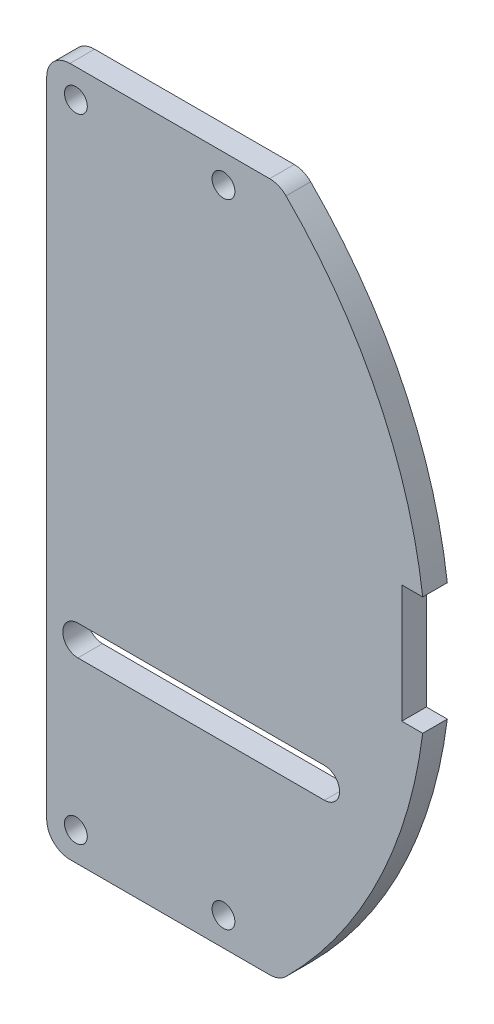
SolidWorks part; units mm, degrees
material "Delrin 2700 NC010, Low Viscosity Acetal Copolymer (SS)"
ref_plane "Front Plane" through (0, 0, 0) normal (0, 0, 1) x (1, 0, 0)
ref_plane "Top Plane" through (0, 0, 0) normal (0, 1, 0) x (1, 0, 0)
ref_plane "Right Plane" through (0, 0, 0) normal (1, 0, 0) x (0, 0, -1)
sketch "Sketch1" plane through (0, 0, 0) normal (0, 0, 1) x (1, 0, 0)
  line L2 (12.5875, 44.5) -> (42.5875, 44.5)
  line L5 (12.5875, -44.5) -> (12.5875, 44.5)
  line L8 (12.5875, -44.5) -> (42.5875, -44.5)
  arc A4 (42.5875, 44.5) -> (42.5875, -44.5) centre (0, 0) cw
  dimension "D2" = 30
extrude "Boss-Extrude1" add sketch "Sketch1" along normal blind 3.175
sketch "Sketch2" plane through (0, 0, 3.175) normal (0, 0, 1) x (1, 0, 0)
  line L0 (12.5875, 0) -> (61.595, 0) construction
  line L1 (12.5875, 44.5) -> (12.5875, -44.5) construction
  circle A0 centre (16.3543, -40.8119) radius 1.4732
  arc A1 (42.5875, -44.5) -> (42.5875, 44.5) centre (0, 0) ccw construction
  circle A2 centre (35.4043, -40.8119) radius 1.4732
  circle A3 centre (16.3543, 40.8119) radius 1.4732
  circle A4 centre (35.4043, 40.8119) radius 1.4732
  dimension "D1" = 2
extrude "Cut-Extrude1" cut sketch "Sketch2" against normal through all
sketch "Sketch3" plane through (0, 0, 3.175) normal (0, 0, 1) x (1, 0, 0)
  line L0 (58.42, 7.62) -> (61.1118, 7.62) construction
  line L1 (58.42, -7.62) -> (61.1118, -7.62) construction
  line L2 (58.42, 7.62) -> (58.42, -7.62) construction
  line L3 (58.42, 7.62) -> (61.1218, 7.62)
  line L4 (58.42, -7.62) -> (61.1218, -7.62)
  line L5 (58.42, 7.62) -> (58.42, -7.62)
  arc A3 (42.5875, -44.5) -> (42.5875, 44.5) centre (0, 0) ccw construction
  arc A4 (61.1218, -7.62) -> (61.1218, 7.62) centre (0, 0) ccw
extrude "Cut-Extrude2" cut sketch "Sketch3" against normal through all
fillet "Fillet1" radius 3 4 edges at (12.5875, -44.5, 1.5875) (42.5875, -44.5, 1.5875) (12.5875, 44.5, 1.5875) (42.5875, 44.5, 1.5875)
sketch "Sketch4" plane through (0, 0, 3.175) normal (0, 0, 1) x (1, 0, 0)
  line L0 (46.9295, -14.42) -> (8.8343, -14.42)
  line L1 (8.8343, -14.42) -> (8.8343, -24.58)
  line L2 (8.8343, -24.58) -> (46.9295, -24.58)
  arc A0 (46.9295, -24.58) -> (46.9295, -14.42) centre (46.9295, -19.5) ccw
extrude "Cut-Extrude3" [suppressed] cut sketch "Sketch4" against normal through all
fillet "Fillet2" [suppressed] radius 3
sketch "Sketch5" plane through (0, 0, 3.175) normal (0, 0, 1) x (1, 0, 0)
  line L0 (16.6122, -19.5) -> (48.4448, -19.5) construction
  line L1 (16.6122, -17.5542) -> (48.4448, -17.5542)
  line L2 (16.6122, -21.4458) -> (48.4448, -21.4458)
  arc A0 (16.6122, -17.5542) -> (16.6122, -21.4458) centre (16.6122, -19.5) ccw
  circle A2 centre (45.3296, -19.5) radius 4.318 construction
  arc A3 (48.4448, -21.4458) -> (48.4448, -17.5542) centre (48.4448, -19.5) ccw
  arc A4 (49.2918, -21.2165) -> (51.8682, -13.8285) centre (-1.4274, 0.6141) ccw construction
  arc A5 (15.5478, -26.4804) -> (48.4448, -23.6057) centre (12.5875, 197.0625) ccw construction
  point P12 (32.5285, -19.5)
  dimension "D1" = 8.636
  dimension "D2" = 31.8326
  dimension "D3" = 3.8915
extrude "Cut-Extrude5" cut sketch "Sketch5" against normal through all
